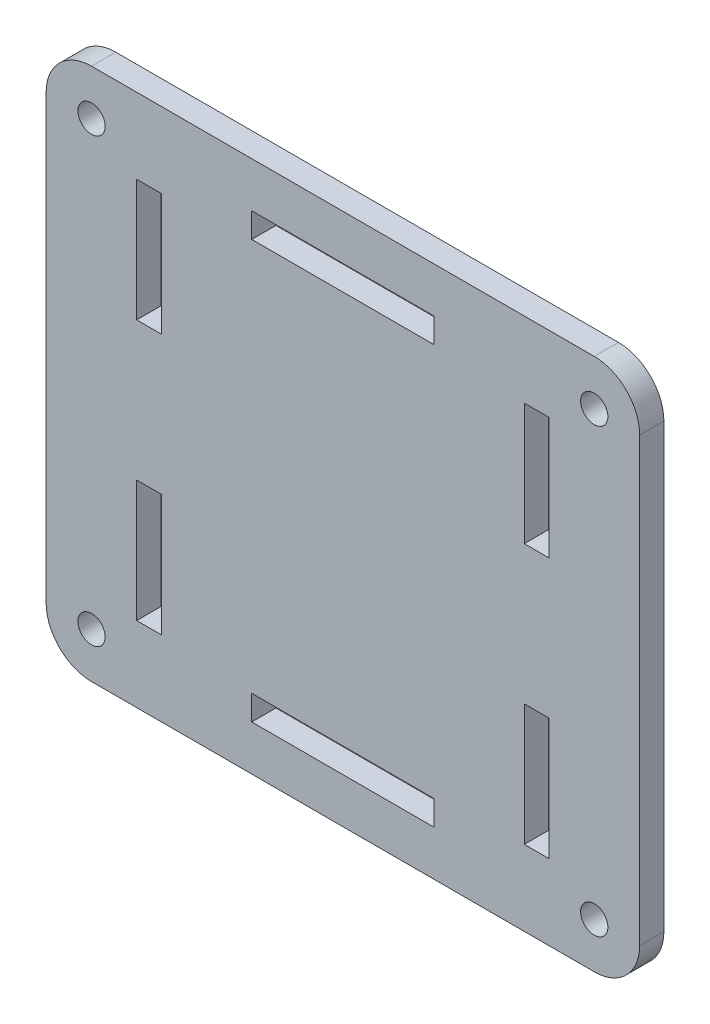
SolidWorks part; units mm, degrees
material "MDF"
ref_plane "正面" through (0, 0, 0) normal (1, 0, 0) x (0, 1, 0)
ref_plane "平面" through (0, 0, 0) normal (0, 0, 1) x (0, 1, 0)
ref_plane "右側面" through (0, 0, 0) normal (0, 1, 0) x (-1, 0, 0)
sketch "ｽｹｯﾁ1" plane through (0, 0, 0) normal (0, 0, 1) x (0, 1, 0)
  line L0 (80.55, 33.95) -> (76.45, 33.95)
  line L1 (0, 0) -> (88, 0)
  line L2 (0, 0) -> (0, 98)
  line L3 (0, 98) -> (88, 98)
  line L4 (88, 0) -> (88, 98)
  line L5 (44, 98) -> (44, 0) construction
  line L6 (0, 49) -> (88, 49) construction
  line L7 (12.45, 78.95) -> (32.55, 78.95)
  line L8 (12.45, 78.95) -> (12.45, 83.05)
  line L9 (12.45, 83.05) -> (32.55, 83.05)
  line L10 (32.55, 78.95) -> (32.55, 83.05)
  line L11 (22.5, 83.05) -> (22.5, 78.95) construction
  line L12 (12.45, 81) -> (32.55, 81) construction
  line L13 (55.45, 78.95) -> (75.55, 78.95)
  line L14 (55.45, 78.95) -> (55.45, 83.05)
  line L15 (55.45, 83.05) -> (75.55, 83.05)
  line L16 (75.55, 78.95) -> (75.55, 83.05)
  line L17 (65.5, 83.05) -> (65.5, 78.95) construction
  line L18 (55.45, 81) -> (75.55, 81) construction
  line L19 (12.45, 14.95) -> (32.55, 14.95)
  line L20 (12.45, 14.95) -> (12.45, 19.05)
  line L21 (12.45, 19.05) -> (32.55, 19.05)
  line L22 (32.55, 14.95) -> (32.55, 19.05)
  line L23 (22.5, 19.05) -> (22.5, 14.95) construction
  line L24 (12.45, 17) -> (32.55, 17) construction
  line L25 (55.45, 14.95) -> (75.55, 14.95)
  line L26 (55.45, 14.95) -> (55.45, 19.05)
  line L27 (55.45, 19.05) -> (75.55, 19.05)
  line L28 (75.55, 14.95) -> (75.55, 19.05)
  line L29 (65.5, 19.05) -> (65.5, 14.95) construction
  line L30 (55.45, 17) -> (75.55, 17) construction
  line L31 (7.45, 64.05) -> (11.55, 64.05)
  line L32 (7.45, 64.05) -> (7.45, 33.95)
  line L33 (7.45, 33.95) -> (11.55, 33.95)
  line L34 (11.55, 64.05) -> (11.55, 33.95)
  line L35 (7.45, 64.05) -> (11.55, 33.95) construction
  line L36 (7.45, 33.95) -> (11.55, 64.05) construction
  line L37 (76.45, 64.05) -> (76.45, 33.95)
  line L38 (80.55, 64.05) -> (76.45, 64.05)
  line L39 (80.55, 64.05) -> (80.55, 33.95)
  point P25 (9.5, 49)
  point P26 (7.45, 49)
  point P49 (22.5, 17)
  point P58 (65.5, 17)
  point P65 (22.5, 81)
  point P70 (65.5, 81)
  point P309 (44, 49)
  dimension "D1" = 88
  dimension "D2" = 98
  dimension "D3" = 20.1
  dimension "D4" = 4.1
  dimension "D5" = 43
  dimension "D6" = 21.5
  dimension "D7" = 64
  dimension "D8" = 32
  dimension "D9" = 30.1
  dimension "D10" = 4.1
  dimension "D11" = 34.5
extrude "ﾎﾞｽ - 押し出し1" add sketch "ｽｹｯﾁ1" along normal blind 4
sketch "ｽｹｯﾁ2" plane through (0, 0, 4) normal (0, 0, 1) x (1, 0, 0)
  line L0 (-98, 0) -> (0, 0) construction
  line L1 (0, 88) -> (-98, 88) construction
  line L2 (-98, 88) -> (-98, 0) construction
  line L3 (0, 0) -> (0, 88) construction
  point P0 (-90.5, 80.5)
  point P1 (-7.5, 80.5)
  point P2 (-7.5, 7.5)
  point P3 (-90.5, 7.5)
  dimension "D1" = 7.5
  dimension "D2" = 7.5
  dimension "D3" = 7.5
  dimension "D4" = 7.5
hole_wizard "M4 すきま穴1" positions "ｽｹｯﾁ2" profile "ｽｹｯﾁ3" hole size "M4" standard "JIS" end condition through all
sketch "ｽｹｯﾁ3" plane through (-90.5, 80.5, 4) normal (1, 0, 0) x (0, -1, 0)
  line L0 (0, 0) -> (0, 4)
  line L1 (0, 4) -> (2.25, 4)
  line L2 (2.25, 4) -> (2.25, 0)
  line L5 (2.25, 0) -> (0, 0)
  line L11 (0, -6.35) -> (0, 107.95) construction
  dimension "通し穴の直径" = 4.5
  dimension "通し穴の深さ" = 4
fillet "ﾌｨﾚｯﾄ3" radius 7.5 4 edges at (-98, 88, 2) (0, 88, 2) (0, 0, 2) (-98, 0, 2)
equation "\"D6@ｽｹｯﾁ1\"= \"D5@ｽｹｯﾁ1\" / 2"
equation "\"D8@ｽｹｯﾁ1\"= \"D7@ｽｹｯﾁ1\" / 2"
equation "\"D4@ｽｹｯﾁ2\"= \"D3@ｽｹｯﾁ2\""
equation "\"D2@ｽｹｯﾁ2\"= \"D1@ｽｹｯﾁ2\""
